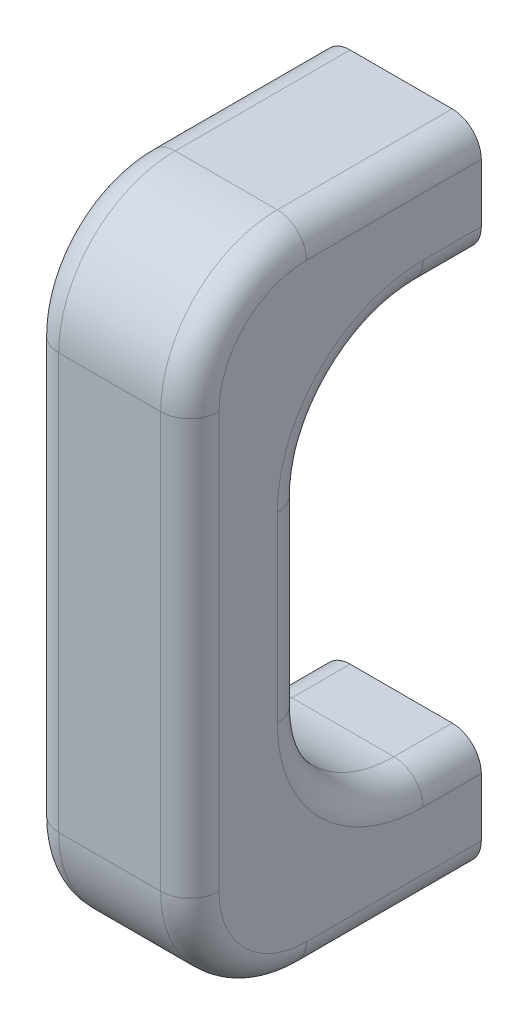
SolidWorks part; units mm, degrees
material "Plastique personnalisé"
ref_plane "Plan de face" through (0, 0, 0) normal (0, 0, 1) x (1, 0, 0)
ref_plane "Plan de dessus" through (0, 0, 0) normal (0, 1, 0) x (1, 0, 0)
ref_plane "Plan de droite" through (0, 0, 0) normal (1, 0, 0) x (0, 0, -1)
sketch "Esquisse1" plane through (0, 0, 0) normal (0, 0, 1) x (1, 0, 0)
  line L1 (-5.5, -22.25) -> (5.5, -22.25)
  line L2 (-5.5, -22.25) -> (-5.5, 22.25)
  line L3 (-5.5, 22.25) -> (5.5, 22.25)
  line L4 (5.5, -22.25) -> (5.5, 22.25)
  line L5 (-5.5, -22.25) -> (5.5, 22.25) construction
  line L6 (-5.5, 22.25) -> (5.5, -22.25) construction
  point P0 (0, 0)
  dimension "D1" = 11
  dimension "D2" = 44.5
extrude "Boss.-Extru.1" add sketch "Esquisse1" along normal blind 20
fillet "Congé1" radius 8 2 edges at (0, -22.25, 20) (0, 22.25, 20)
sketch "Esquisse2" plane through (5.5, 0, 0) normal (1, 0, 0) x (0, 0, -1)
  line L0 (0, 22.25) -> (0, 14.2505) construction
  line L1 (0, -22.25) -> (0, 22.25) construction
  line L2 (0, 14.2505) -> (-11.9999, 14.2505) construction
  line L3 (0, 0) -> (16.0731, 0) construction
  line L4 (0, -14.2505) -> (-11.9999, -14.2505) construction
  line L6 (-11.9999, 14.2505) -> (0, 14.2505)
  line L7 (-11.9999, 14.2505) -> (-11.9999, -14.2505)
  line L8 (-11.9999, -14.2505) -> (0, -14.2505)
  line L9 (0, 14.2505) -> (0, -14.2505)
extrude "Enlèv. mat.-Extru.1" cut sketch "Esquisse2" against normal blind 20
fillet "Congé2" radius 8 2 edges at (0, -14.2505, 11.9999) (0, 14.2505, 11.9999)
sketch "Esquisse3" plane through (0, 0, 0) normal (0, 0, -1) x (-1, 0, 0)
  line L0 (5.5, 22.25) -> (-5.5, 14.2505) construction
  line L1 (-5.5, -14.2505) -> (5.5, -22.25) construction
  circle A0 centre (0, 18.2503) radius 1.5
  circle A1 centre (0, -18.2503) radius 1.5
extrude "Enlèv. mat.-Extru.2" cut sketch "Esquisse3" against normal blind 7
fillet "Congé3" radius 2 20 edges at (5.5, -14.2505, 1.9999) (5.5, -11.9074, 9.6567) (5.5, 0, 11.9999) (5.5, 14.2505, 1.9999) (-5.5, 14.2505, 1.9999) (-5.5, -14.2505, 1.9999) (-5.5, -11.9074, 9.6567) (-5.5, 0, 11.9999) (5.5, 22.25, 6) (5.5, -22.25, 6) (5.5, -19.9069, 17.6569) (5.5, 0, 20) (-5.5, -22.25, 6) (-5.5, -19.9069, 17.6569) (-5.5, 0, 20) (-5.5, 22.25, 6) (5.5, 11.9074, 9.6567) (-5.5, 11.9074, 9.6567) (5.5, 19.9069, 17.6569) (-5.5, 19.9069, 17.6569)
